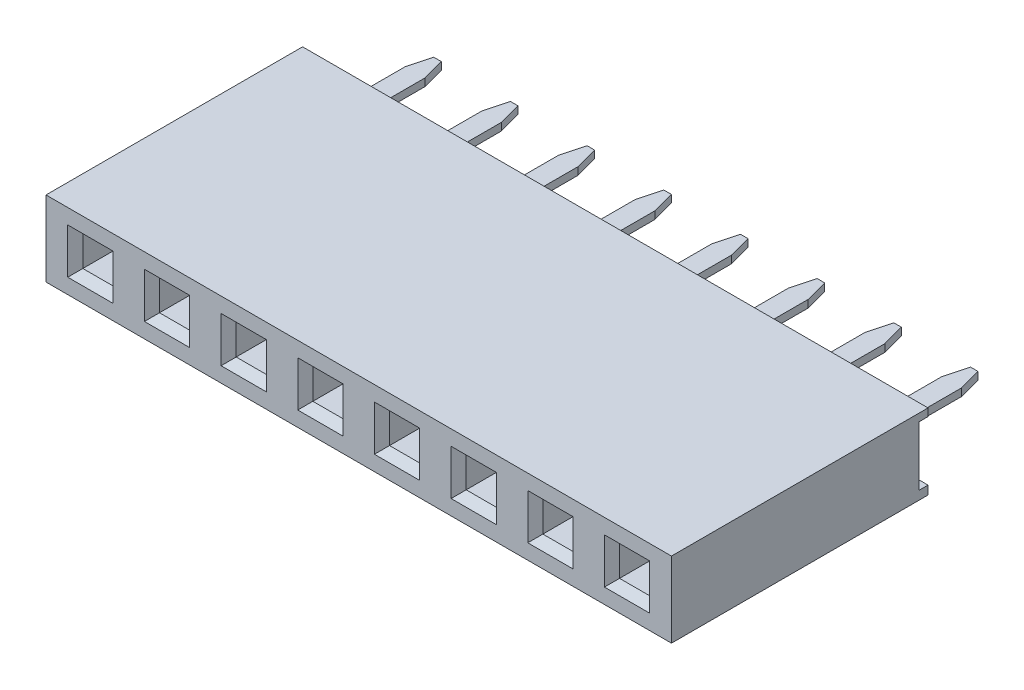
SolidWorks part; units mm, degrees
ref_plane "Front Plane" through (0, 0, 0) normal (0, 0, 1) x (1, 0, 0)
ref_plane "Top Plane" through (0, 0, 0) normal (0, 1, 0) x (1, 0, 0)
ref_plane "Right Plane" through (0, 0, 0) normal (1, 0, 0) x (0, 0, -1)
sketch "Sketch1" plane through (0, 0, 0) normal (0, 0, 1) x (1, 0, 0)
  line L1 (0, 0) -> (20.72, 0)
  line L2 (0, 0) -> (0, 2.5)
  line L3 (0, 2.5) -> (20.72, 2.5)
  line L4 (20.72, 0) -> (20.72, 2.5)
  dimension "width" = 2.5
  dimension "length" = 20.72
extrude "Boss-Extrude1" add sketch "Sketch1" along normal blind 8.5
sketch "Sketch2" plane through (0, 0, 8.5) normal (0, 0, 1) x (1, 0, 0)
  line L0 (0, 1.25) -> (20.72, 1.25) construction
  line L1 (0, 2.5) -> (0, 0) construction
  line L2 (20.72, 0) -> (20.72, 2.5) construction
  line L3 (0, 0) -> (20.72, 0) construction
  line L5 (20.72, 2.5) -> (0, 2.5) construction
  line L6 (1.47, 2.5) -> (1.47, 0) construction
  line L7 (0.97, 1.75) -> (1.97, 1.75)
  line L8 (0.97, 1.75) -> (0.97, 0.75)
  line L9 (0.97, 0.75) -> (1.97, 0.75)
  line L10 (1.97, 1.75) -> (1.97, 0.75)
  point P16 (1.47, 1.75)
  point P17 (1.97, 1.25)
  dimension "D1" = 1.25
  dimension "D2" = 1.47
  dimension "D3" = 1
  dimension "D4" = 1
extrude "Cut-Extrude1" cut sketch "Sketch2" against normal blind 2.25
chamfer "Chamfer1" distance 0.25 angle 45 4 edges at (0.97, 1.25, 8.5) (1.47, 0.75, 8.5) (1.97, 1.25, 8.5) (1.47, 1.75, 8.5)
sketch "Sketch3" plane through (0, 0, 0) normal (-1, 0, 0) x (0, 0, 1)
  line L0 (0, 2.5) -> (0, 0) construction
  line L1 (0, 2.25) -> (0.3, 2.25)
  line L2 (0, 2.25) -> (0, 0.2861)
  line L3 (0, 0.2861) -> (0.3, 0.2861)
  line L4 (0.3, 2.25) -> (0.3, 0.2861)
  line L5 (8.5, 1.25) -> (0, 1.2681) construction
  line L6 (8.5, 2.5) -> (0, 2.5) construction
  line L7 (8.5, 2.5) -> (8.5, 0) construction
  dimension "D1" = 0.25
  dimension "D2" = 0.3
extrude "Cut-Extrude2" cut sketch "Sketch3" against normal through all
ref_plane "Plane1" through (0, 1.25, 0) normal (0, -1, 0) x (-1, 0, 0)
sketch "Sketch4" plane through (0, 1.25, 0) normal (0, -1, 0) x (-1, 0, 0)
  line L0 (-1.47, -8.25) -> (-1.47, -0.3) construction
  line L1 (-0.97, -8.25) -> (-1.97, -8.25) construction
  line L2 (-20.72, -0.3) -> (0, -0.3) construction
  line L3 (0, 0) -> (-20.72, 0) construction
  line L4 (-1.795, -0.3) -> (-1.145, -0.3)
  line L5 (-1.795, -0.3) -> (-1.795, 3)
  line L6 (-1.795, 3) -> (-1.145, 3)
  line L7 (-1.145, -0.3) -> (-1.145, 3)
  point P10 (-1.47, -0.3)
  dimension "D1" = 0.65
  dimension "D2" = 3
extrude "Boss-Extrude2" add sketch "Sketch4" along normal mid plane 0.25 separate body
chamfer "Chamfer2" distance 0.2 angle 75 2 edges at (1.145, 1.25, -3) (1.795, 1.25, -3)
pattern_linear "LPattern4" count 8 spacing 2.54 along (1, 0, 0) of bodies 104
pattern_linear "LPattern5" count 8 spacing 2.54 along (1, 0, 0) of "Cut-Extrude1", "Chamfer1"
equation "\"pins\" = 8"
equation "\"rows\"= 1"
equation "\"length\"= 2.54 * \"pins\" + .4"
equation "\"width\"= 2.5 * \"rows\""
equation "\"width@Sketch1\"= 2.5 * \"rows\""
equation "\"length@Sketch1\"= 2.54 * \"pins\" + .4"
equation "\"D2@LPattern5\"= \"rows\""
equation "\"D2@LPattern4\"= \"rows\""
equation "\"D1@LPattern4\"= \"pins\""
equation "\"D1@LPattern5\"= \"pins\""
